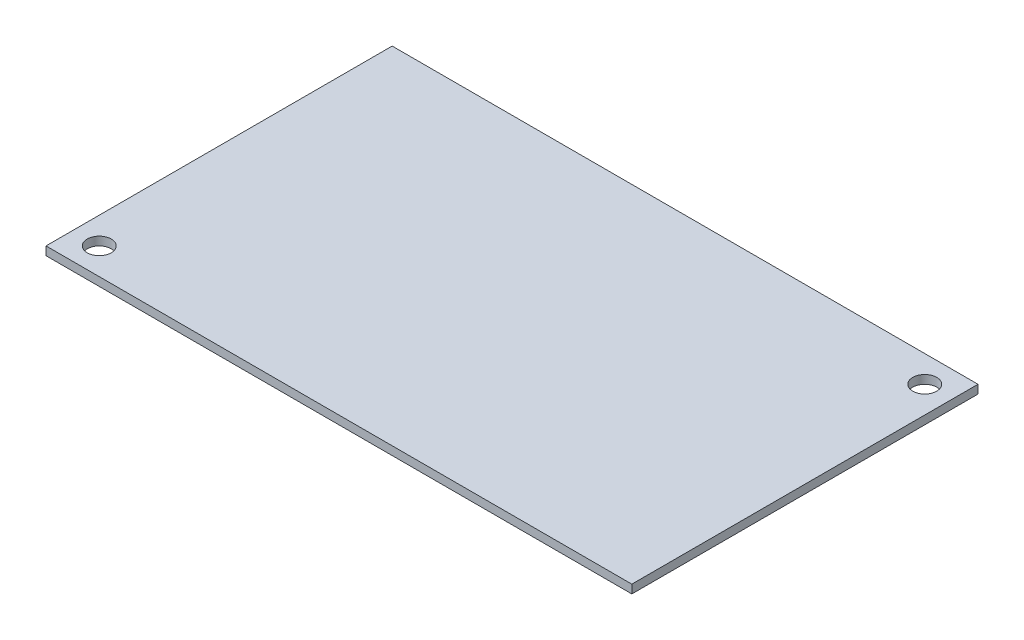
SolidWorks part; units mm, degrees
ref_plane "Front" through (0, 0, 0) normal (0, 0, 1) x (1, 0, 0)
ref_plane "Top" through (0, 0, 0) normal (0, 1, 0) x (1, 0, 0)
ref_plane "Right" through (0, 0, 0) normal (1, 0, 0) x (0, 0, -1)
sketch "Sketch1" plane through (0, 0, 0) normal (0, 1, 0) x (1, 0, 0)
  line L1 (0, 0) -> (110, 0)
  line L2 (0, 0) -> (0, 65)
  line L3 (0, 65) -> (110, 65)
  line L4 (110, 0) -> (110, 65)
  dimension "D1" = 110
  dimension "D2" = 65
extrude "Boss-Extrude1" add sketch "Sketch1" along normal blind 1.6
hole_wizard "M4 Clearance Hole1" positions "Sketch2" profile "Sketch3" hole size "M4" standard "ANSI Metric"
sketch "Sketch2" plane through (0, 1.6, 0) normal (0, 1, 0) x (1, 0, 0)
  line L0 (0, 65) -> (0, 0) construction
  line L1 (0, 0) -> (110, 0) construction
  line L2 (110, 0) -> (110, 65) construction
  line L3 (110, 65) -> (0, 65) construction
  point P0 (5, 5)
  point P2 (105, 60)
  dimension "D1" = 5
  dimension "D2" = 5
  dimension "D3" = 5
  dimension "D4" = 5
sketch "Sketch3" plane through (5, 1.6, -5) normal (1, 0, 0) x (0, 0, 1)
  line L0 (0, 0) -> (0, 11.4519)
  line L1 (0, 11.4519) -> (2.25, 10.1)
  line L2 (2.25, 10.1) -> (2.25, 0)
  line L5 (2.25, 0) -> (0, 0)
  line L10 (0, 11.4519) -> (-2.25, 10.1) construction
  line L11 (0, -6.35) -> (0, 107.95) construction
  dimension "Hole Dia." = 4.5
  dimension "Hole Depth" = 10.1
  dimension "Drill Angle" = 118
